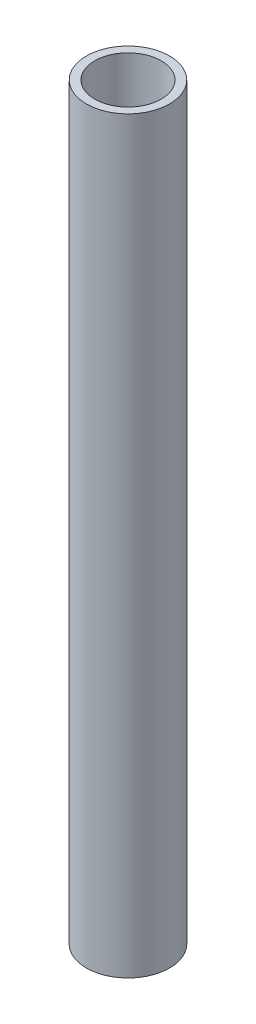
SolidWorks part; units mm, degrees
ref_plane "Alzado" through (0, 0, 0) normal (0, 0, 1) x (1, 0, 0)
ref_plane "Planta" through (0, 0, 0) normal (0, 1, 0) x (1, 0, 0)
ref_plane "Vista lateral" through (0, 0, 0) normal (1, 0, 0) x (0, 0, -1)
sketch "Croquis1" plane through (0, 0, 0) normal (0, 1, 0) x (1, 0, 0)
  circle A0 centre (0, 0) radius 25
  circle A1 centre (0, 0) radius 20
  dimension "D1" = 50
  dimension "D2" = 40
extrude "Saliente-Extruir1" add sketch "Croquis1" along normal blind 450
